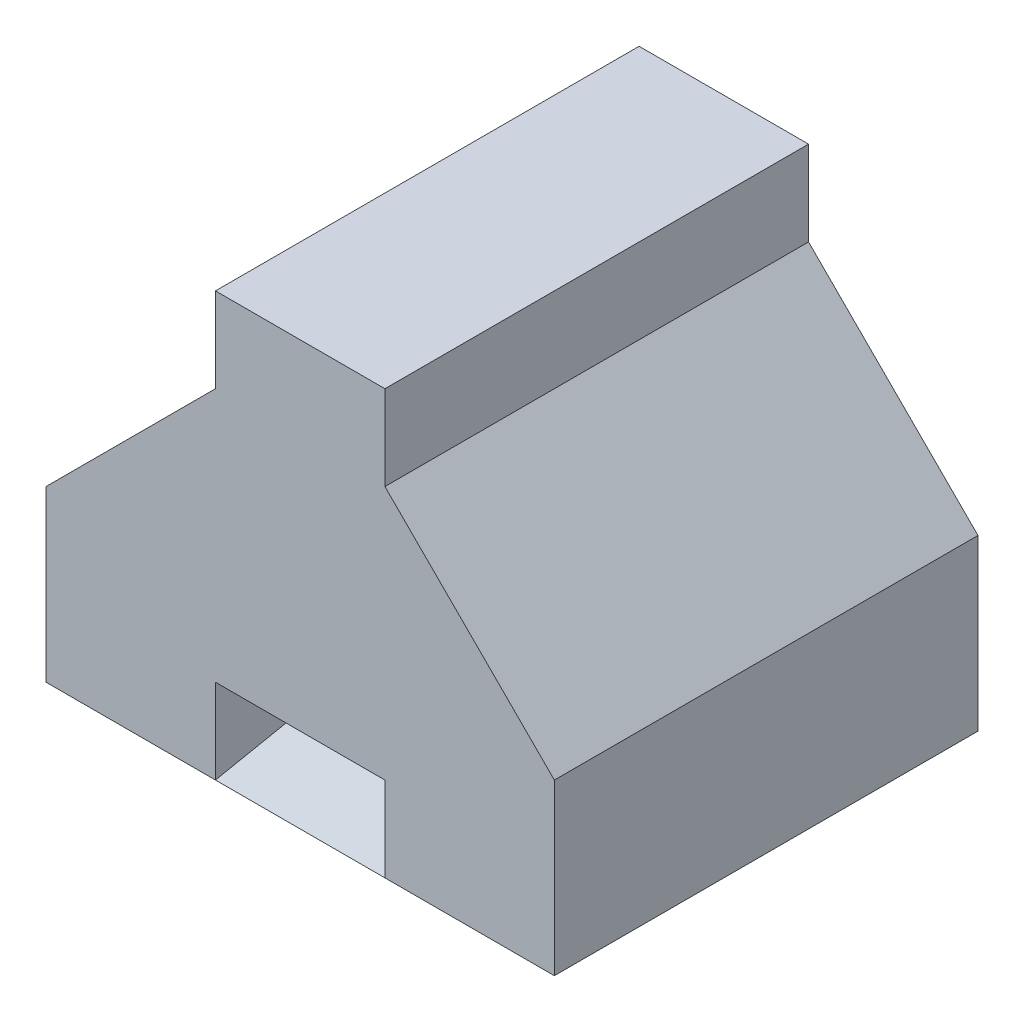
SolidWorks part; units mm, degrees
ref_plane "Front Plane" through (0, 0, 0) normal (0, 0, 1) x (1, 0, 0)
ref_plane "Top Plane" through (0, 0, 0) normal (0, 1, 0) x (1, 0, 0)
ref_plane "Right Plane" through (0, 0, 0) normal (1, 0, 0) x (0, 0, -1)
sketch "Sketch1" plane through (0, 0, 0) normal (0, 0, 1) x (1, 0, 0)
  line L0 (-30, 0) -> (-30, 10)
  line L1 (-30, 10) -> (-20, 20)
  line L2 (-20, 20) -> (-20, 25)
  line L3 (-20, 25) -> (-10, 25)
  line L4 (-10, 25) -> (-10, 20)
  line L5 (-10, 20) -> (0, 10)
  line L6 (0, 10) -> (0, 0)
  line L7 (0, 0) -> (-30, 0)
  dimension "D1" = 10
  dimension "D2" = 5
  dimension "D3" = 5
  dimension "D4" = 10
  dimension "D5" = 10
  dimension "D6" = 30
  dimension "D7" = 10
  dimension "D8" = 10
extrude "Boss-Extrude1" add sketch "Sketch1" along normal blind 25
sketch "Sketch2" plane through (0, 0, 25) normal (0, 0, 1) x (1, 0, 0)
  line L0 (-20, 0) -> (-20, 5)
  line L1 (-30, 0) -> (0, 0) construction
  line L2 (-20, 5) -> (-10, 5)
  line L3 (-10, 5) -> (-10, 0)
  line L4 (-10, 0) -> (-20, 0)
  dimension "D1" = 10
  dimension "D2" = 10
  dimension "D3" = 5
extrude "Cut-Extrude1" cut sketch "Sketch2" against normal blind 46
sketch "Sketch3" plane through (-20, 0, 0) normal (1, 0, 0) x (0, 0, -1)
  line L0 (-25, 0) -> (0, 5)
  line L1 (0, 5) -> (0, 0)
  line L2 (0, 0) -> (-25, 0)
extrude "Boss-Extrude3" add sketch "Sketch3" along normal blind 10 separate body
